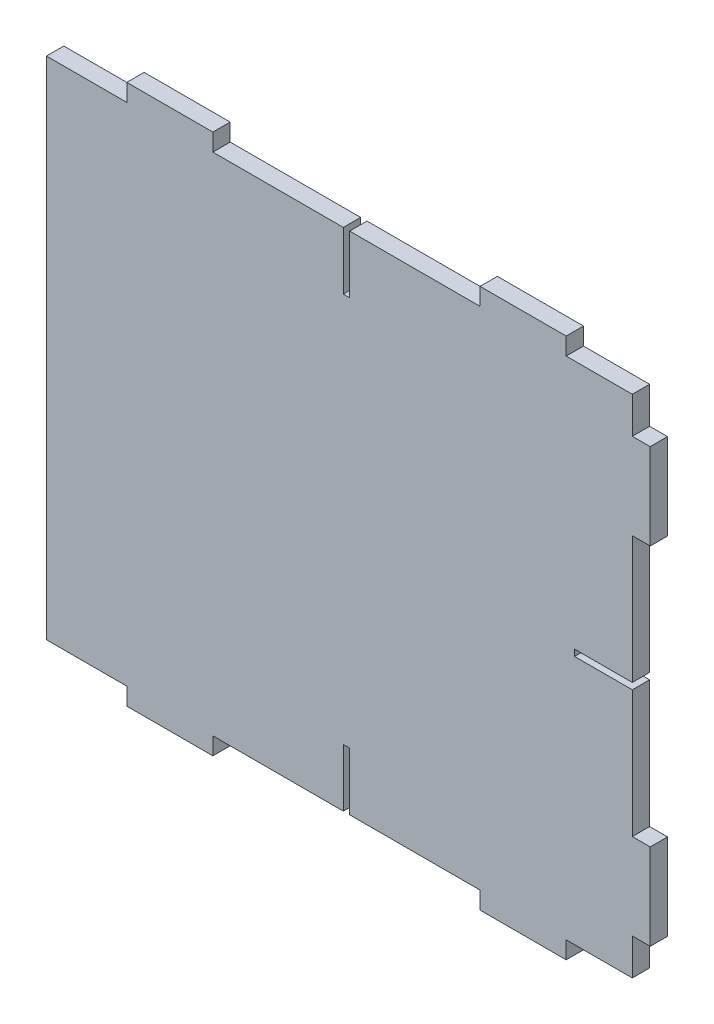
SolidWorks part; units mm, degrees
ref_plane "Plano frontal" through (0, 0, 0) normal (0, 0, 1) x (1, 0, 0)
ref_plane "Plano superior" through (0, 0, 0) normal (0, 1, 0) x (1, 0, 0)
ref_plane "Plano direito" through (0, 0, 0) normal (1, 0, 0) x (0, 0, -1)
sketch "Esboço1" plane through (0, 0, 0) normal (0, 0, 1) x (1, 0, 0)
  line L1 (209, 0) -> (0, 0)
  line L2 (209, 0) -> (209, 187)
  line L3 (209, 187) -> (0, 187)
  line L4 (0, 0) -> (0, 187)
  line L6 (0, 187) -> (209, 187)
  line L7 (0, 187) -> (0, 181)
  line L8 (0, 181) -> (209, 181)
  line L9 (209, 187) -> (209, 181)
  line L10 (209, 187) -> (202.8, 187)
  line L11 (209, 187) -> (209, 0)
  line L12 (209, 0) -> (202.8, 0)
  line L13 (202.8, 187) -> (202.8, 0)
  line L15 (27.8053, 181) -> (57.6053, 181)
  line L16 (27.8053, 181) -> (27.8053, 187)
  line L17 (27.8053, 187) -> (57.6053, 187)
  line L18 (57.6053, 181) -> (57.6053, 187)
  line L19 (150.1053, 181) -> (179.9053, 181)
  line L20 (150.1053, 181) -> (150.1053, 187)
  line L21 (150.1053, 187) -> (179.9053, 187)
  line L22 (179.9053, 181) -> (179.9053, 187)
  line L23 (202.8, 168.4) -> (209, 168.4)
  line L24 (202.8, 168.4) -> (202.8, 138.6)
  line L25 (202.8, 138.6) -> (209, 138.6)
  line L26 (209, 168.4) -> (209, 138.6)
  line L27 (202.8, 48.4) -> (209, 48.4)
  line L28 (202.8, 48.4) -> (202.8, 18.6)
  line L29 (202.8, 18.6) -> (209, 18.6)
  line L30 (209, 48.4) -> (209, 18.6)
  line L39 (0, 93.5) -> (202.8, 93.5) construction
  line L40 (179.9053, 6) -> (179.9053, 0)
  line L41 (150.1053, 0) -> (179.9053, 0)
  line L42 (150.1053, 6) -> (150.1053, 0)
  line L43 (150.1053, 6) -> (179.9053, 6)
  line L44 (57.6053, 6) -> (57.6053, 0)
  line L45 (27.8053, 0) -> (57.6053, 0)
  line L46 (27.8053, 6) -> (27.8053, 0)
  line L47 (27.8053, 6) -> (57.6053, 6)
  line L48 (0, 0) -> (0, 6)
  line L50 (0, 0) -> (209, 0)
  line L51 (0, 0) -> (0, 6)
  line L52 (0, 6) -> (209, 6)
  line L53 (209, 0) -> (209, 6)
  dimension "D2" = 6
  dimension "D3" = 29.8
  dimension "D4" = 27.8053
  dimension "D5" = 29.8
  dimension "D6" = 92.5
  dimension "D7" = 187
  dimension "D8" = 6.2
  dimension "D9" = 18.6
  dimension "D10" = 29.8
  dimension "D11" = 18.6
  dimension "D12" = 48.4
  dimension "D13" = 209
extrude "Ressalto-extrusão1" add sketch "Esboço1" along normal blind 6 contours L13 L8 L4 L1 | L8 L18 L3 L16 | L8 L22 L3 L20 | L13 L25 L11 L23 | L13 L29 L11 L27 | L39 L4 L52 L47 L43 L13 | L47 L46 L1 L44 | L43 L42 L1 L40
sketch "Esboço2" plane through (0, 0, 6) normal (0, 0, 1) x (1, 0, 0)
  line L0 (103.8579, 181) -> (103.8579, 6) construction
  line L1 (202.8, 92.4) -> (103.8579, 92.4) construction
  line L2 (202.8, 138.6) -> (202.8, 48.4) construction
  line L3 (202.8, 93.5) -> (103.8579, 93.5) construction
  line L5 (102.7579, 181) -> (102.7579, 6)
  line L6 (202.8, 94.6) -> (103.8579, 94.6)
  line L7 (104.9579, 181) -> (104.9579, 6)
  line L8 (202.8, 92.4) -> (103.8579, 92.4)
  line L10 (102.7579, 161) -> (182.8, 161)
  line L11 (102.7579, 161) -> (102.7579, 26)
  line L12 (102.7579, 26) -> (182.8, 26)
  line L13 (182.8, 161) -> (182.8, 26)
  line L17 (0, 6) -> (0, 181) construction
  line L18 (103.8579, 187) -> (103.8579, 6) construction
  line L20 (104.9579, 187) -> (104.9579, 6) construction
  line L21 (57.6053, 181) -> (150.1053, 181) construction
  line L22 (102.7579, 187) -> (102.7579, 6) construction
  line L23 (57.6053, 6) -> (150.1053, 6) construction
  line M8 (57.6053, 6) -> (150.1053, 6)
  line M17 (202.8, 48.4) -> (202.8, 138.6)
  line M26 (150.1053, 181) -> (57.6053, 181)
  dimension "D3" = 103.8579
  dimension "D4" = 20
  dimension "D5" = 20
  dimension "D6" = 20
  dimension "D1" = 1.1
  dimension "D2" = 1.1
extrude "Corte-extrusão1" cut sketch "Esboço2" against normal blind 6 contours L5 L10 L7 M26 | L6 L13 L8 M17 | L12 L5 L7 M8
